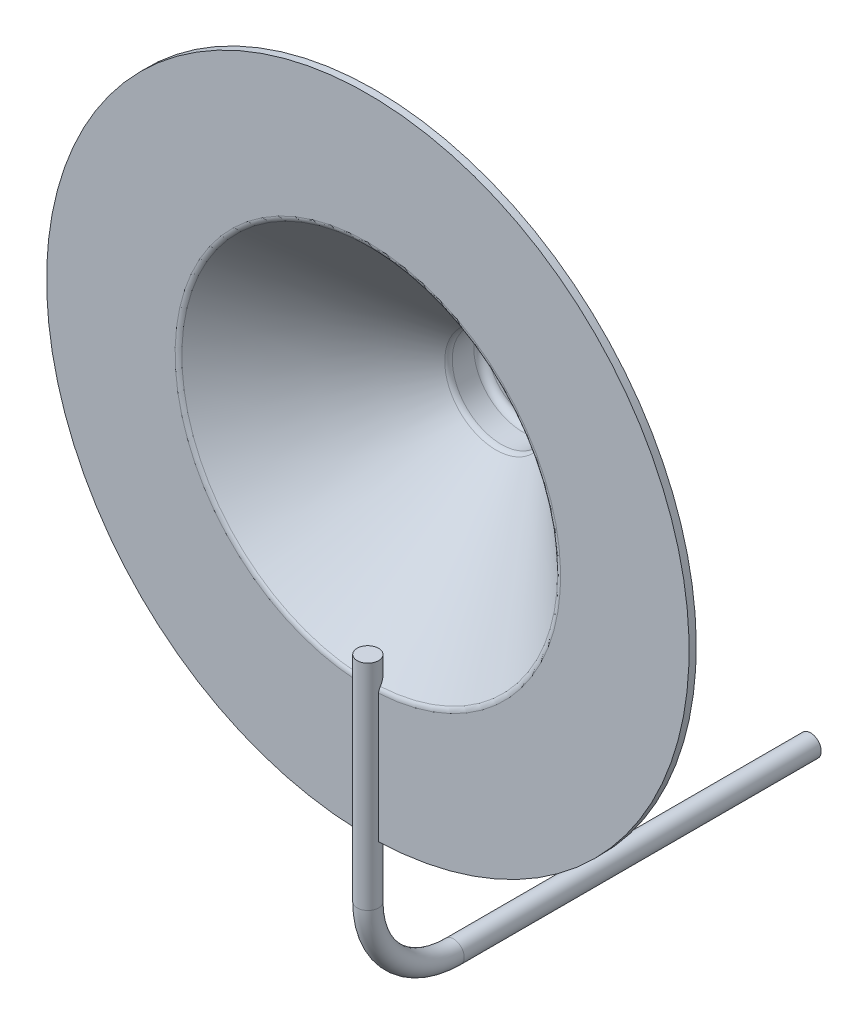
SolidWorks part; units mm, degrees
material "Chrome Stainless Steel"
ref_plane "Front Plane" through (0, 0, 0) normal (0, 0, 1) x (1, 0, 0)
ref_plane "Top Plane" through (0, 0, 0) normal (0, 1, 0) x (1, 0, 0)
ref_plane "Right Plane" through (0, 0, 0) normal (1, 0, 0) x (0, 0, -1)
ref_plane "Plane1" through (0, 0, 0) normal (0, 0, 1) x (1, 0, 0)
sketch "Sketch3" plane through (0, 0, 0) normal (0, 0, 1) x (1, 0, 0)
  circle A0 centre (0, -6.5) radius 0.15
  dimension "D1" = 0.3
ref_plane "Plane2" through (0, 0, 0) normal (1, 0, 0) x (0, 0, -1)
sketch "Sketch4" plane through (0, 0, 0) normal (1, 0, 0) x (0, 0, -1)
  line L0 (0, -6.5) -> (-5, -6.5)
  line L1 (0, -6.35) -> (0, -6.65) construction
  line L2 (-6.2, -5.3) -> (-6.2, -2.3)
  line L3 (0.8, 2.2961) -> (0.8, -2.2961) construction
  arc A0 (-5, -6.5) -> (-6.2, -5.3) centre (-5, -5.3) cw
  dimension "D2" = 1.2
  dimension "D1" = 7
  dimension "D3" = 3
sweep "Sweep1" add profiles "Sketch3" path "Sketch4"
sketch "Sketch6" plane through (0, 0, 0) normal (1, 0, 0) x (0, 0, -1)
  line L0 (-6.2, -2.3) -> (-6.2, 0) construction
  line L1 (-6.05, -2.3) -> (-6.35, -2.3) construction
  line L2 (-6.2, 0) -> (-3.9312, 0) construction
  line L3 (-6.2, -4.5) -> (-6.2, -2.7)
  line L4 (-6.1734, -2.6321) -> (-4.4047, -0.7186)
  line L5 (-4.3312, -0.6865) -> (-4.0312, -0.6865)
  line L6 (-3.9312, -0.5865) -> (-3.9312, 0)
  line L7 (-3.9312, 0) -> (-3.8312, 0)
  line L8 (-6.1, -4.5) -> (-6.1, -2.7)
  line L9 (-6.1, -2.7) -> (-4.3312, -0.7865)
  line L10 (-4.3312, -0.7865) -> (-4.0312, -0.7865)
  line L11 (-3.8312, -0.5865) -> (-3.8312, 0)
  line L12 (-6.2, -4.5) -> (-6.1, -4.5)
  line L13 (-3.8312, -0.5865) -> (-3.8312, -0.1) construction
  line L14 (-3.8312, -0.1) -> (-3.7915, -0.1) construction
  line L15 (-3.9312, 0) -> (-3.7915, 0) construction
  arc A0 (-6.2, -2.7) -> (-6.1734, -2.6321) centre (-6.1, -2.7) cw
  arc A1 (-4.4047, -0.7186) -> (-4.3312, -0.6865) centre (-4.3312, -0.7865) cw
  arc A2 (-4.0312, -0.6865) -> (-3.9312, -0.5865) centre (-4.0312, -0.5865) ccw
  arc A3 (-6.1, -2.7) -> (-6.1, -2.7) centre (-6.1, -2.7) cw
  arc A4 (-4.3312, -0.7865) -> (-4.3312, -0.7865) centre (-4.3312, -0.7865) cw
  arc A5 (-4.0312, -0.7865) -> (-3.8312, -0.5865) centre (-4.0312, -0.5865) ccw
  point P13 (-6.2, -2.6609)
  dimension "D1" = 0.1
  dimension "D3" = 4.5
  dimension "D4" = 1.8
  dimension "D5" = 2.3688
  dimension "D6" = 0.3
  dimension "D2" = 0.1
revolve "Revolve1" add sketch "Sketch6" angle 360 about L2
